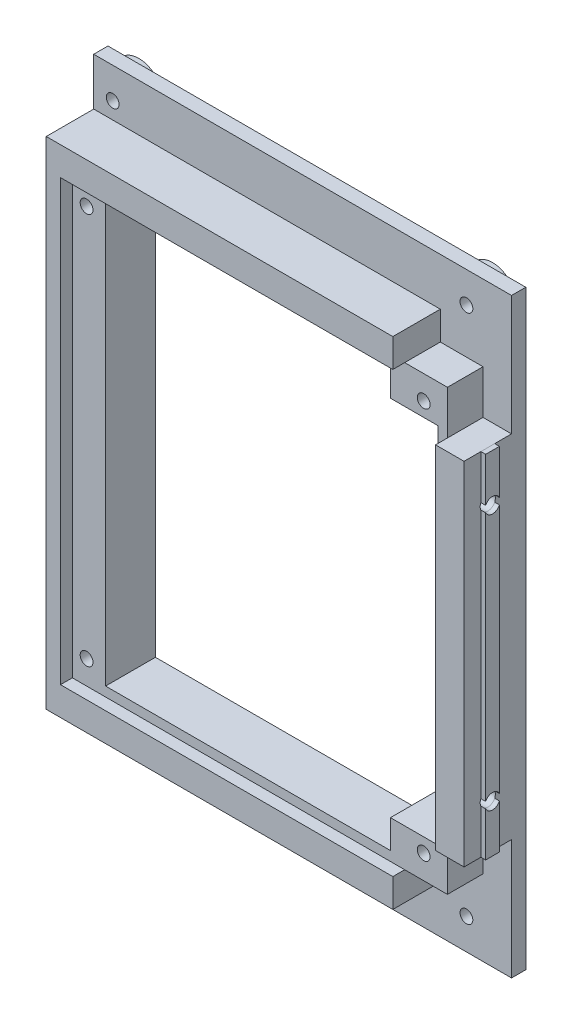
SolidWorks part; units mm, degrees
ref_plane "Plan de face" through (0, 0, 0) normal (0, 0, 1) x (1, 0, 0)
ref_plane "Plan de dessus" through (0, 0, 0) normal (0, 1, 0) x (1, 0, 0)
ref_plane "Plan de droite" through (0, 0, 0) normal (1, 0, 0) x (0, 0, -1)
sketch "Main-Sketch" plane through (0, 0, 0) normal (0, 0, 1) x (1, 0, 0)
  line L1 (-44, -62.25) -> (44, -62.25)
  line L2 (-44, -62.25) -> (-44, 62.25)
  line L3 (-44, 62.25) -> (44, 62.25)
  line L4 (44, -62.25) -> (44, 62.25)
  point P5 (-21.6785, -5.2182)
  point P6 (-44, 0)
  point P8 (0, -62.25)
  dimension "D1" = 88
  dimension "D2" = 124.5
extrude "Main-Extrusion" add sketch "Main-Sketch" along normal blind 13
sketch "Fix-Sketch" plane through (0, 0, 0) normal (0, 0, 1) x (1, 0, 0)
  line L0 (44, 62.25) -> (-44, 62.25) construction
  line L2 (-44, 62.25) -> (-44, -62.25) construction
  line L3 (-44, -62.25) -> (44, -62.25) construction
  circle A0 centre (-40, 55.75) radius 1.35
  circle A1 centre (-40, -55.75) radius 1.35
  circle A2 centre (34.5, -55.75) radius 1.35
  circle A3 centre (34.5, 55.75) radius 1.35
  circle A4 centre (-40, 55.75) radius 5
  circle A5 centre (34.5, 55.75) radius 5
  circle A6 centre (34.5, -55.75) radius 5
  circle A7 centre (-40, -55.75) radius 5
  circle A8 centre (12.5, -55.75) radius 1.35
  circle A9 centre (12.5, -55.75) radius 5
  point P21 (0, 0)
  dimension "D1" = 6.5
  dimension "D2" = 2.7
  dimension "D3" = 111.5
  dimension "D7" = 10
  dimension "D4" = 4
  dimension "D5" = 6.5
  dimension "D6" = 74.5
  dimension "D8" = 22
extrude "Board Plot" add sketch "Fix-Sketch" against normal blind 2.5
sketch "Esquisse1" plane through (0, 0, 0) normal (0, 0, -1) x (-1, 0, 0)
  circle A0 centre (-34.5, 55.75) radius 1.35
  circle A1 centre (40, 55.75) radius 1.35
  circle A2 centre (40, -55.75) radius 1.35
  circle A3 centre (-12.5, -55.75) radius 1.35
  circle A4 centre (-34.5, -55.75) radius 1.35
  circle A5 centre (-12.5, -55.75) radius 1.35 construction
extrude "Board Plot Hole" cut sketch "Esquisse1" against normal through all
sketch "Esquisse2" plane through (0, 0, 0) normal (0, -1, 0) x (1, 0, 0)
  line L0 (44, 13) -> (44, 0) construction
  line L1 (44, 9.45) -> (45, 9.45)
  line L2 (44, 9.45) -> (44, 6.55)
  line L3 (44, 6.55) -> (45, 6.55)
  line L4 (45, 9.45) -> (45, 6.55)
  line L5 (-44, 13) -> (-44, 0) construction
  line L6 (-44, 9.45) -> (-45, 9.45)
  line L7 (-44, 9.45) -> (-44, 6.55)
  line L8 (-44, 6.55) -> (-45, 6.55)
  line L9 (-45, 9.45) -> (-45, 6.55)
  line L10 (44, 13) -> (-44, 13) construction
  point P12 (45, 14.6606)
  dimension "D1" = 1
  dimension "D2" = 2.9
  dimension "D3" = 3.55
extrude "MakerBeam Fixing" add sketch "Esquisse2" against normal mid plane 74 separate body
sketch "Esquisse3" plane through (0, 0, 13) normal (0, 0, 1) x (1, 0, 0)
  line L1 (-34, 44.25) -> (26, 44.25)
  line L2 (-34, 44.25) -> (-34, -44.25)
  line L3 (-34, -44.25) -> (26, -44.25)
  line L4 (26, 44.25) -> (26, 38.25)
  line L5 (44, 62.25) -> (-44, 62.25) construction
  line L7 (-44, -62.25) -> (44, -62.25) construction
  line L9 (-44, 62.25) -> (-44, -62.25) construction
  line L11 (26, 38.25) -> (36, 38.25)
  line L12 (36, 38.25) -> (36, -38.25)
  line L13 (36, -38.25) -> (26, -38.25)
  line L14 (26, -38.25) -> (26, -44.25)
  line L16 (44, -62.25) -> (44, 62.25) construction
  point P14 (35.1795, -41.25)
  dimension "D1" = 18
  dimension "D2" = 10
  dimension "D3" = 6
  dimension "D4" = 18
  dimension "D5" = 60
  dimension "D6" = 88.5
  dimension "D7" = 10
  dimension "D8" = 8
extrude "Window Hole" cut sketch "Esquisse3" against normal through all
sketch "Esquisse4" plane through (0, 0, 13) normal (0, 0, 1) x (1, 0, 0)
  line L0 (44, 62.25) -> (44, 37)
  line L2 (44, 37) -> (38, 37)
  line L3 (38, 37) -> (38, 46.25)
  line L4 (29, 46.25) -> (38, 46.25)
  line L5 (-44, 52.25) -> (-44, 62.25)
  line L6 (44, 62.25) -> (-44, 62.25) construction
  line L7 (-44, 62.25) -> (44, 62.25)
  line L8 (44, -62.25) -> (44, 62.25) construction
  line L9 (44, -62.25) -> (44, -37)
  line L10 (44, -37) -> (38, -37)
  line L11 (38, -37) -> (38, -46.25)
  line L12 (38, -46.25) -> (29, -46.25)
  line L13 (29, 52.25) -> (29, 46.25)
  line L14 (29, -46.25) -> (29, -52.25)
  line L15 (-44, -62.25) -> (44, -62.25)
  line L16 (29, 52.25) -> (-44, 52.25)
  line L18 (29, -52.25) -> (-44, -52.25)
  line L19 (-44, -62.25) -> (44, -62.25) construction
  line L20 (-44, -52.25) -> (-44, -62.25)
  line L21 (-44, 124.5) -> (-44, -124.5) construction
  line L23 (44, -62.25) -> (44, 62.25) construction
  point P2 (44, -36.8771)
  point P3 (-44, 52)
  point P9 (33.5, 46.25)
  point P10 (-44.7447, -62.25)
  point P15 (44, -36.5)
  point P19 (39, -46.7436)
  point P20 (-45, 52)
  point P22 (0, 0)
  point P24 (44, 62.25)
  point P25 (44, 37)
  point P29 (45, -37)
  point P30 (45, -11.75)
  point P32 (42.4971, -36.5)
  point P33 (0, 0)
  point P36 (27.1958, -28)
  point P37 (0, 0)
  point P38 (0, 0)
  point P39 (-44, -52)
  point P40 (45, -37)
  point P41 (45, -37)
  point P44 (44, -36.5)
  point P45 (0, 0)
  point P46 (0, 0)
  point P47 (41.3174, -36.5)
  point P48 (0, 0)
  point P49 (-44, -36.5)
  point P50 (42.0269, -36.5)
  point P51 (-40.3684, -36.5)
  point P52 (-44, -62.25)
  point P55 (44, -62.25)
  point P56 (45.7399, 45.5006)
  point P57 (43.3127, 52.3663)
  point P58 (44, 62.25)
  point P60 (44, 52.3918)
  point P63 (0, 0)
  point P64 (44, -37)
  dimension "D1" = 6
  dimension "D2" = 6
  dimension "D3" = 15
  dimension "D4" = 10
  dimension "D5" = 25.25
  dimension "D6" = 10
  dimension "D7" = 25.25
  dimension "D8" = 104.5
extrude "External Hole" cut sketch "Esquisse4" against normal blind 10
sketch "Esquisse5" plane through (45, 0, 0) normal (1, 0, 0) x (0, 0, -1)
  line L1 (-13, -37) -> (-3, -37) construction
  line L2 (-9.45, 37) -> (-6.55, 37) construction
  circle A0 centre (-8, 27) radius 1.6
  circle A1 centre (-8, -27) radius 1.6
  point P4 (0, 0)
  point P7 (0, 0)
  point P10 (0, 0)
  point P11 (-8, 37)
  dimension "D1" = 3.2
  dimension "D2" = 10
  dimension "D3" = 10
extrude "MakerBeam Fixing Hole" cut sketch "Esquisse5" against normal up to next
sketch "Esquisse7" plane through (0, 0, 13) normal (0, 0, 1) x (1, 0, 0)
  line L0 (38, -46.25) -> (29, -46.25) construction
  line L1 (-41, 46.25) -> (38, 46.25)
  line L2 (-41, 46.25) -> (-41, -46.25)
  line L3 (-41, -46.25) -> (38, -46.25)
  line L4 (38, 46.25) -> (38, -46.25)
  line L6 (-44, 52.25) -> (-44, -52.25) construction
  point P6 (38, 46.25)
  point P8 (-44, 46.25)
  point P9 (-40.5579, 46.25)
  dimension "D1" = 3
extrude "Glass Hole" cut sketch "Esquisse7" against normal blind 2.5
sketch "Esquisse8" plane through (0, 0, 10.5) normal (0, 0, 1) x (1, 0, 0)
  line L0 (29, 46.25) -> (-41, 46.25) construction
  line L1 (-41, 46.25) -> (-41, -46.25) construction
  line L2 (38, 37) -> (38, 46.25) construction
  line L3 (-41, -46.25) -> (29, -46.25) construction
  circle A0 centre (-38, 41.25) radius 1.35
  circle A1 centre (33, 41.25) radius 1.35
  circle A2 centre (33, -41.25) radius 1.35
  circle A3 centre (-38, -41.25) radius 1.35
  point P8 (0, 0)
  point P11 (0, 0)
  point P14 (0, 0)
  point P17 (0, 0)
  point P18 (0, 0)
  point P19 (0, 0)
  dimension "D1" = 2.7
  dimension "D2" = 5
  dimension "D3" = 3
  dimension "D4" = 5
  dimension "D5" = 5
extrude "Glass Fixing Hole" cut sketch "Esquisse8" against normal through all and the other way through all
